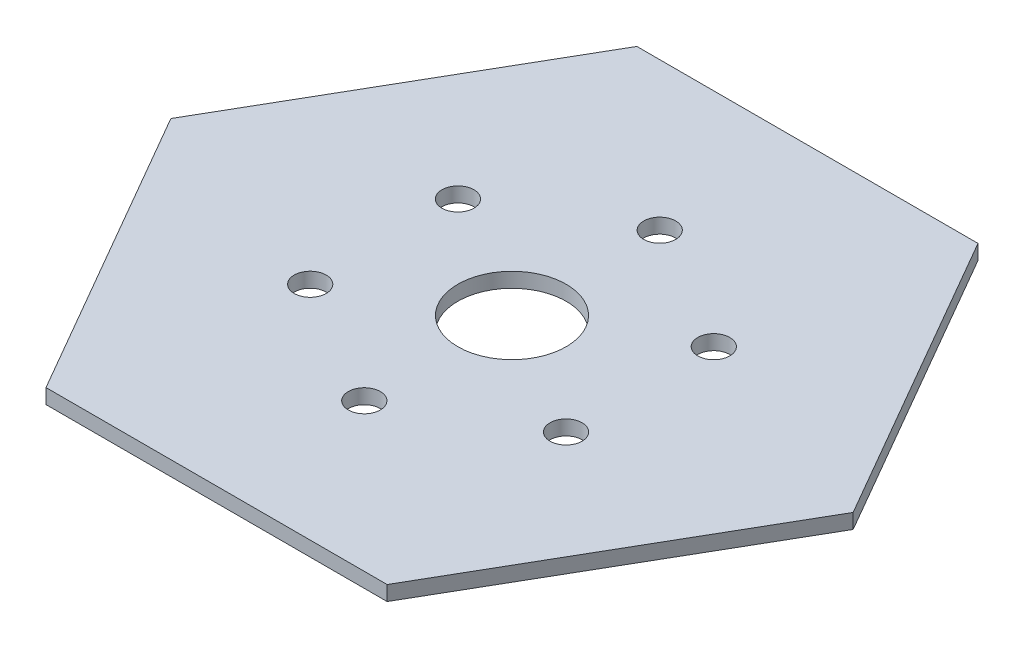
SolidWorks part; units mm, degrees
ref_plane "Alzado" through (0, 0, 0) normal (0, 0, 1) x (1, 0, 0)
ref_plane "Planta" through (0, 0, 0) normal (0, 1, 0) x (1, 0, 0)
ref_plane "Vista lateral" through (0, 0, 0) normal (1, 0, 0) x (0, 0, -1)
sketch "Croquis1" plane through (0, 0, 0) normal (0, 1, 0) x (1, 0, 0)
  line L1 (69.282, 0) -> (34.641, 60)
  line L2 (34.641, 60) -> (-34.641, 60)
  line L3 (-34.641, 60) -> (-69.282, 0)
  line L4 (-69.282, 0) -> (-34.641, -60)
  line L5 (-34.641, -60) -> (34.641, -60)
  line L6 (34.641, -60) -> (69.282, 0)
  circle A0 centre (0, 0) radius 11
  circle A1 centre (0, 0) radius 60 construction
  dimension "D1" = 22
  dimension "D2" = 120
extrude "Saliente-Extruir1" add sketch "Croquis1" along normal blind 3
sketch "Croquis2" plane through (0, 3, 0) normal (0, 1, 0) x (1, 0, 0)
  line L0 (0, 0) -> (0, 156.286) construction
  circle A0 centre (0, 30) radius 3.25
  circle A1 centre (25.9808, 15) radius 3.25
  circle A2 centre (25.9808, -15) radius 3.25
  circle A3 centre (0, -30) radius 3.25
  circle A4 centre (-25.9808, -15) radius 3.25
  circle A5 centre (-25.9808, 15) radius 3.25
  point P18 (0, 0)
  dimension "D1" = 6.5
  dimension "D2" = 30
  dimension "D3" = 6
extrude "Cortar-Extruir1" cut sketch "Croquis2" against normal through all
